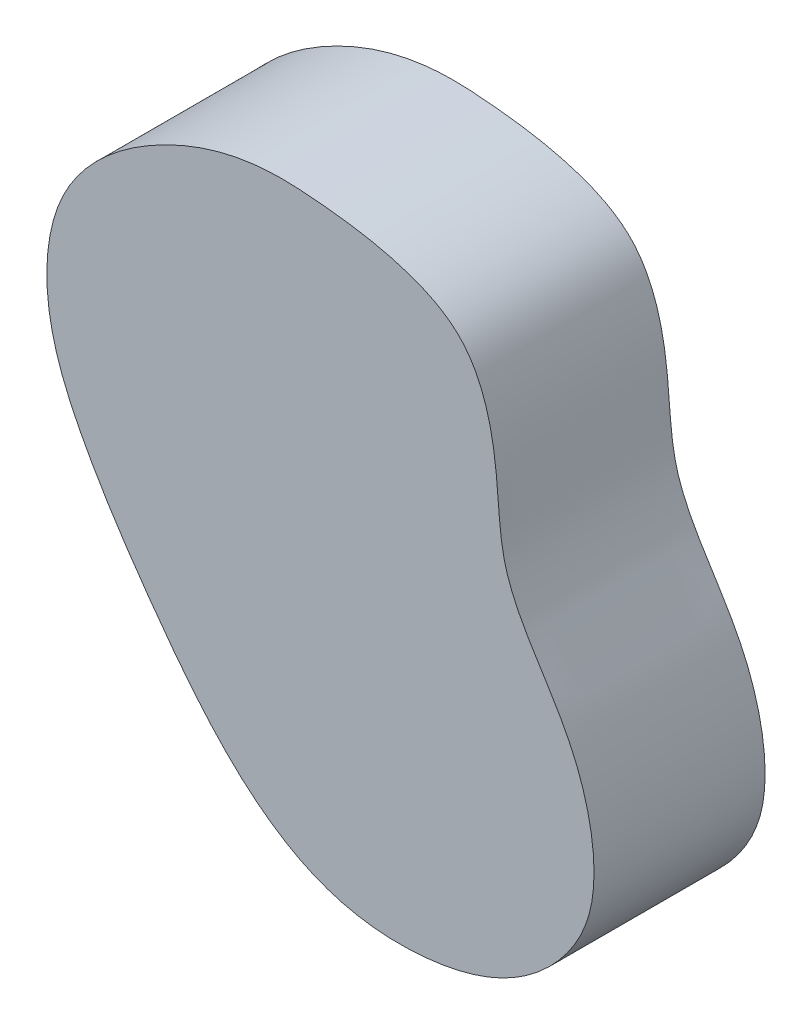
SolidWorks part; units mm, degrees
ref_plane "Front Plane" through (0, 0, 0) normal (0, 0, 1) x (1, 0, 0)
ref_plane "Top Plane" through (0, 0, 0) normal (0, 1, 0) x (1, 0, 0)
ref_plane "Right Plane" through (0, 0, 0) normal (1, 0, 0) x (0, 0, -1)
sketch "Sketch2" plane through (0, 0, 0) normal (0, 0, 1) x (1, 0, 0)
  spline S0 degree 3 poles (18.0808, 82.9641) (11.6451, 82.5747) (1.9631, 79.3683) (-9.5216, 69.9093) (-10.4578, 55.123) (-4.9801, 43.1045) (4.4405, 29.0683) (15.2707, 15.5891) (28.4089, 11.88) (38.5896, 12.6334) (46.0867, 15.7088) (51.7784, 21.3982) (54.9721, 28.9382) (53.5436, 38.309) (49.0195, 47.2736) (43.6309, 54.3263) (42.9991, 62.8533) (42.4288, 69.7981) (39.6688, 77.7751) (31.0868, 81.5149) (23.7015, 82.5593) (18.0808, 82.9641) (11.6451, 82.5747) (1.9631, 79.3683) knots -0.184774 -0.12964 -0.099238 -0.081261 -0.013508 0.083479 0.165992 0.232521 0.32006 0.472533 0.538005 0.583308 0.635794 0.683072 0.727263 0.797572 0.836188 0.913693 0.949936 0.987074 1.041895 1.090371 1.145505 1.175907 1.193884 1.261636 1.358624 1.441137 only from (14.4126, 82.6881) to (14.4126, 82.6881)
  point P21 (17.3903, 82.8542)
extrude "Boss-Extrude1" add sketch "Sketch2" along normal blind 20
